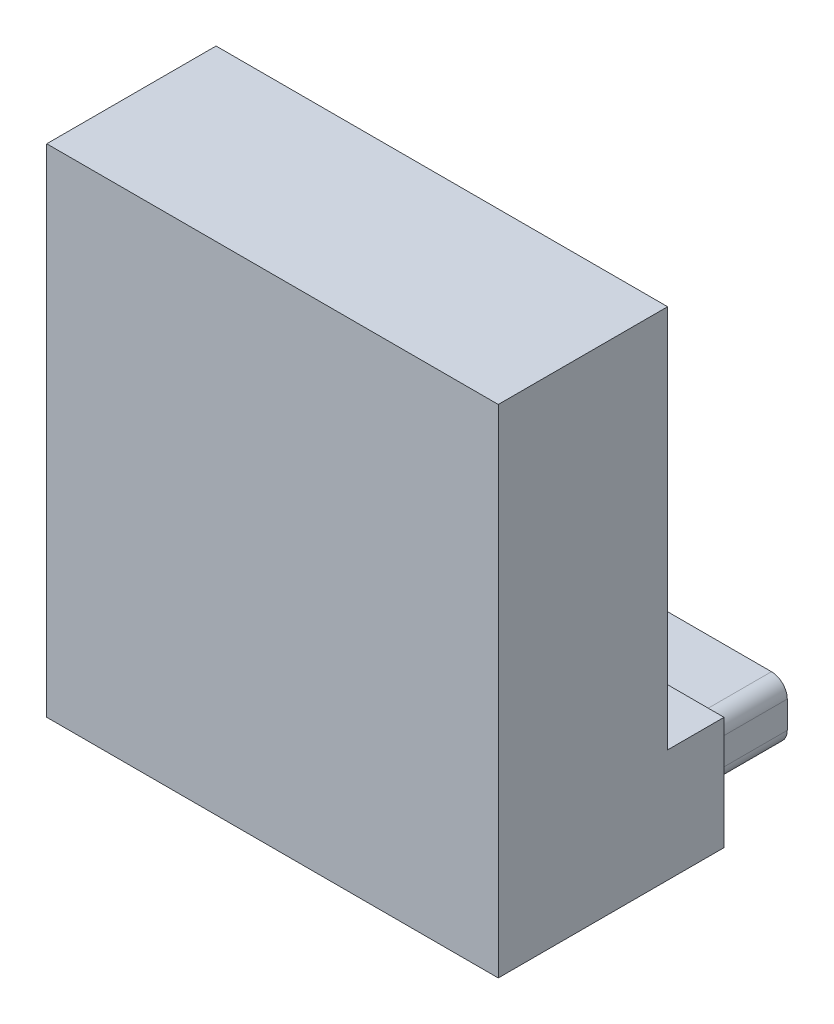
SolidWorks part; units mm, degrees
ref_plane "Front Plane" through (0, 0, 0) normal (0, 0, 1) x (1, 0, 0)
ref_plane "Top Plane" through (0, 0, 0) normal (0, 1, 0) x (1, 0, 0)
ref_plane "Right Plane" through (0, 0, 0) normal (1, 0, 0) x (0, 0, -1)
sketch "Sketch1" plane through (0, 0, 0) normal (0, 1, 0) x (1, 0, 0)
  line L1 (10, -5) -> (-10, -5)
  line L2 (10, -5) -> (10, 5)
  line L3 (10, 5) -> (-10, 5)
  line L4 (-10, -5) -> (-10, 5)
  line L5 (10, -5) -> (-10, 5) construction
  line L6 (10, 5) -> (-10, -5) construction
  point P0 (0, 0)
  dimension "D1" = 20
  dimension "D2" = 10
extrude "Boss-Extrude1" add sketch "Sketch1" along normal blind 5 contours L1 L4 L3 L2
sketch "Sketch2" plane through (0, 0, -5) normal (0, 0, -1) x (-1, 0, 0)
  line L0 (10, 5) -> (10, 0) construction
  line L1 (8.8, 3.8) -> (-8.8, 3.8)
  line L2 (8.8, 3.8) -> (8.8, 1.2)
  line L3 (8.8, 1.2) -> (-8.8, 1.2)
  line L4 (-8.8, 3.8) -> (-8.8, 1.2)
  line L5 (-10, 0) -> (10, 0) construction
  line L6 (-10, 5) -> (10, 5) construction
  line L7 (-10, 5) -> (-10, 0) construction
  dimension "D1" = 1.2
  dimension "D2" = 1.2
  dimension "D3" = 1.2
  dimension "D4" = 1.2
extrude "Boss-Extrude2" add sketch "Sketch2" along normal blind 4 contours L1 L4 L3 L2
fillet "Fillet1" radius 0.7 4 edges at (8.8, 1.2, -7) (8.8, 3.8, -7) (-8.8, 1.2, -7) (-8.8, 3.8, -7)
sketch "Sketch3" plane through (0, 5, 0) normal (0, 1, 0) x (1, 0, 0)
  line L0 (10, -5) -> (10, 5) construction
  line L1 (-10, -5) -> (10, -5)
  line L2 (-10, -5) -> (-10, 2.5)
  line L3 (-10, 2.5) -> (10, 2.5)
  line L4 (10, -5) -> (10, 2.5)
  line L5 (10, 5) -> (-10, 5) construction
  dimension "D1" = 2.5
extrude "Boss-Extrude3" add sketch "Sketch3" along normal blind 17
sketch "Sketch4" plane through (0, 0, -2.5) normal (0, 0, -1) x (-1, 0, 0)
  line L1 (10, 22) -> (10, 5) construction
  line L2 (-10, 5) -> (10, 5) construction
  circle A0 centre (0, 12) radius 2.1
  dimension "D1" = 7
  dimension "D2" = 10
extrude "Boss-Extrude4" add sketch "Sketch4" along normal up to surface (6.5 mm away) contours A0 up to face at (0, 2.5, -9)
ref_plane "Plane1" through (0, 17, 0) normal (0, -1, 0) x (-1, 0, 0)
sketch "Sketch5" plane through (10, 0, 0) normal (1, 0, 0) x (0, 0, -1)
  circle A0 centre (2.5, 22) radius 5
extrude "Cut-Extrude1" [suppressed] cut sketch "Sketch5" against normal through all
